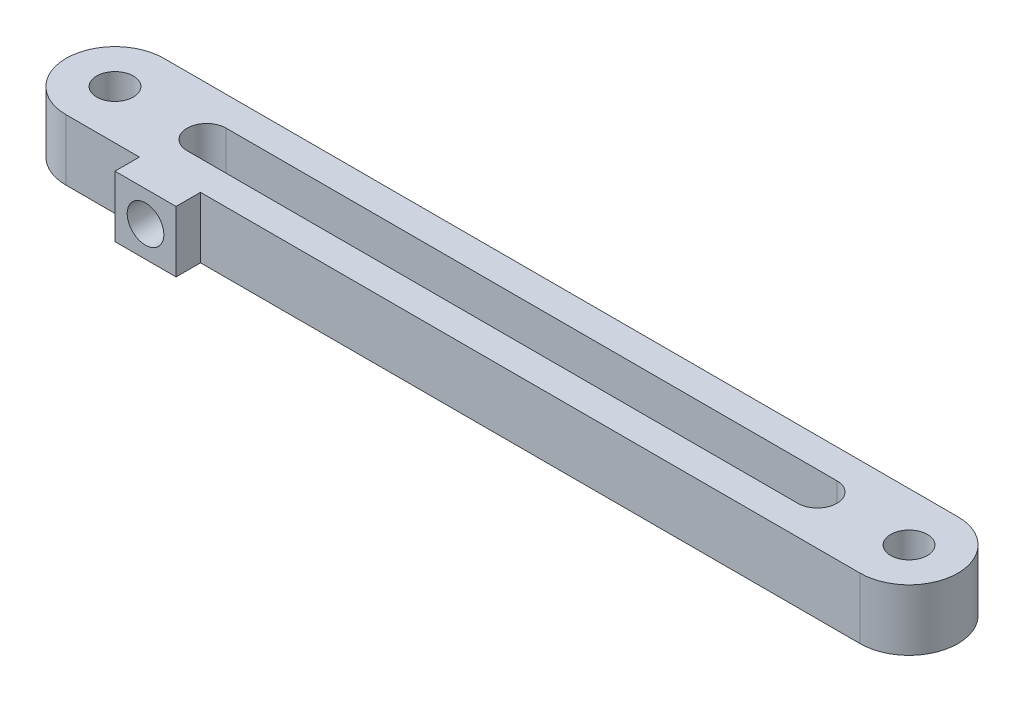
SolidWorks part; units mm, degrees
ref_plane "Front Plane" through (0, 0, 0) normal (0, 0, 1) x (1, 0, 0)
ref_plane "Top Plane" through (0, 0, 0) normal (0, 1, 0) x (1, 0, 0)
ref_plane "Right Plane" through (0, 0, 0) normal (1, 0, 0) x (0, 0, -1)
sketch "Sketch1" plane through (0, 0, 0) normal (0, 1, 0) x (1, 0, 0)
  line L0 (-32.5, 0) -> (32.5, 0) construction
  line L1 (-32.5, 4) -> (32.5, 4)
  line L2 (-32.5, -4) -> (32.5, -4)
  line L3 (-25, 0) -> (25, 0) construction
  line L4 (-25, 1.6) -> (25, 1.6)
  line L5 (-25, -1.6) -> (25, -1.6)
  arc A0 (-32.5, 4) -> (-32.5, -4) centre (-32.5, 0) ccw
  arc A1 (32.5, -4) -> (32.5, 4) centre (32.5, 0) ccw
  circle A2 centre (-32.5, 0) radius 1.5
  circle A3 centre (32.5, 0) radius 1.5
  arc A6 (-25, 1.6) -> (-25, -1.6) centre (-25, 0) ccw
  arc A7 (25, -1.6) -> (25, 1.6) centre (25, 0) ccw
  point P3 (0, 0)
  point P14 (0, 0)
  dimension "D2" = 4
  dimension "D3" = 3
  dimension "D1" = 65
  dimension "D4" = 3.2
  dimension "D5" = 50
extrude "Boss-Extrude1" add sketch "Sketch1" along normal blind 5
sketch "Sketch2" plane through (0, 0, 4) normal (0, 0, 1) x (1, 0, 0)
  line L2 (-32.5, 5) -> (32.5, 5) construction
  line L3 (-26.5, 5) -> (-21.5, 5)
  line L4 (-26.5, 5) -> (-26.5, 0)
  line L5 (-26.5, 0) -> (-21.5, 0)
  line L6 (-21.5, 5) -> (-21.5, 0)
  line L7 (-32.5, 0) -> (32.5, 0) construction
  line L8 (-32.5, 5) -> (-32.5, 0) construction
  dimension "D1" = 6
  dimension "D2" = 5
extrude "Boss-Extrude2" add sketch "Sketch2" along normal blind 2
sketch "Sketch3" plane through (0, 0, 6) normal (0, 0, 1) x (1, 0, 0)
  line L0 (-26.5, 5) -> (-26.5, 0) construction
  line L1 (-21.5, 5) -> (-26.5, 5) construction
  circle A0 centre (-24, 2.5) radius 1.5
  dimension "D1" = 3
  dimension "D2" = 2.5
  dimension "D3" = 2.5
extrude "Cut-Extrude2" cut sketch "Sketch3" against normal blind 3
